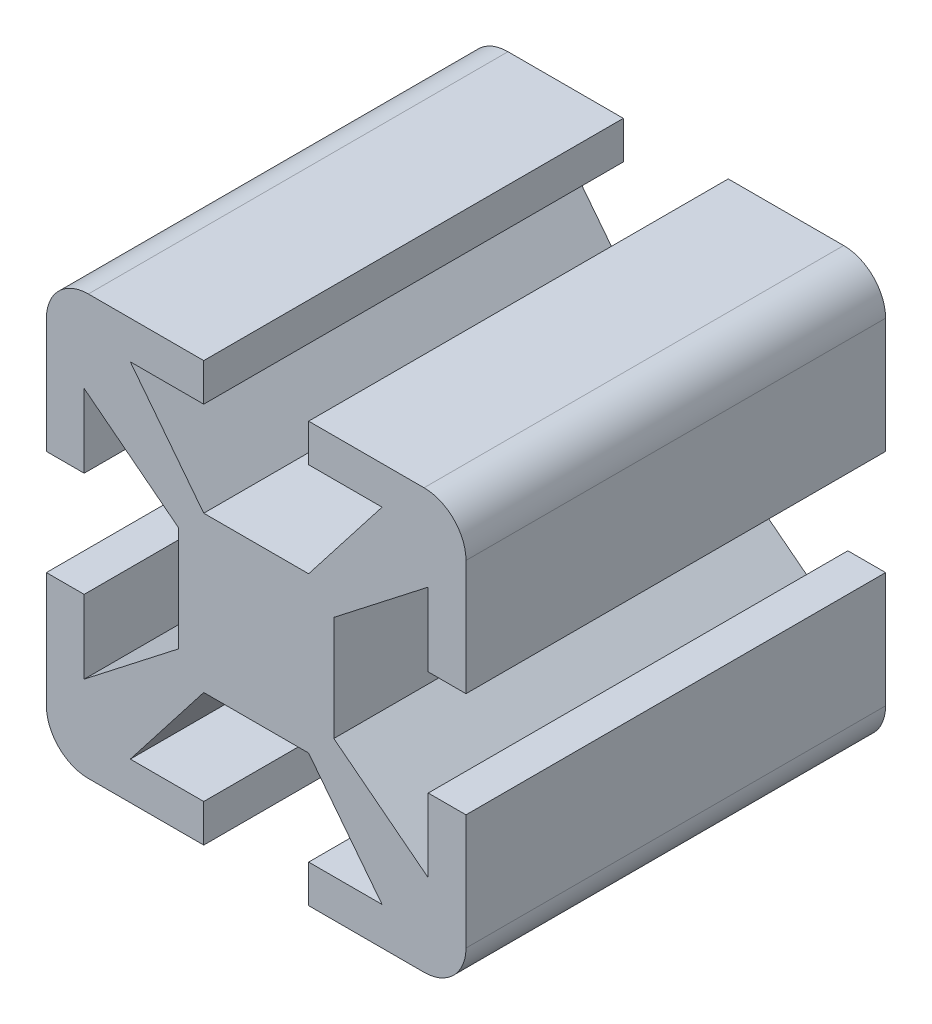
SolidWorks part; units mm, degrees
ref_plane "Plan de face" through (0, 0, 0) normal (0, 0, 1) x (1, 0, 0)
ref_plane "Plan de dessus" through (0, 0, 0) normal (0, 1, 0) x (1, 0, 0)
ref_plane "Plan de droite" through (0, 0, 0) normal (1, 0, 0) x (0, 0, -1)
sketch "Esquisse1" plane through (0, 0, 0) normal (0, 0, 1) x (1, 0, 0)
  line L0 (-10, 8) -> (-10, -8)
  line L1 (-8, 10) -> (8, 10)
  line L2 (-8, -10) -> (8, -10)
  line L3 (10, 8) -> (10, -8)
  line L4 (-8, 8) -> (8, -8) construction
  line L5 (8, 8) -> (-8, -8) construction
  arc A0 (-8, 10) -> (-10, 8) centre (-8, 8) ccw
  arc A1 (8, 10) -> (10, 8) centre (8, 8) cw
  arc A2 (10, -8) -> (8, -10) centre (8, -8) cw
  arc A3 (-8, -10) -> (-10, -8) centre (-8, -8) cw
  point P12 (0, 0)
  dimension "D1" = 2
  dimension "D2" = 2
  dimension "D4" = 2
  dimension "D3" = 20
extrude "Extrusion1" add sketch "Esquisse1" along normal blind 20
sketch "Esquisse3" plane through (0, 0, 20) normal (0, 0, 1) x (1, 0, 0)
  line L0 (10, 2.5) -> (8.2, 2.5)
  line L2 (8.2, 2.5) -> (8.2, 6)
  line L3 (3.7, 2.5) -> (3.7, -2.5)
  line L4 (8.2, -6) -> (8.2, -2.5)
  line L5 (8.2, -2.5) -> (10, -2.5)
  line L6 (10, -8) -> (10, 8) construction
  line L7 (8.2, 6) -> (3.7, 2.5)
  line L8 (10, 2.5) -> (10, -2.5)
  line L9 (8.2, -6) -> (3.7, -2.5)
  point P4 (10, 0)
  point P10 (10, 0)
  dimension "D1" = 5
  dimension "D2" = 1.8
  dimension "D3" = 6.3
  dimension "D4" = 12
  dimension "D5" = 5
extrude "Enlèv. mat.-Extru.1" cut sketch "Esquisse3" against normal blind 300
sketch "Esquisse4" plane through (0, 0, 20) normal (0, 0, 1) x (1, 0, 0)
  line L0 (-10, 2.5) -> (-8.2, 2.5)
  line L1 (-10, 8) -> (-10, -8) construction
  line L2 (-8.2, 2.5) -> (-8.2, 6)
  line L3 (-8.2, 6) -> (-3.7, 2.5)
  line L4 (-3.7, 2.5) -> (-3.7, -2.5)
  line L5 (-8.2, -2.5) -> (-8.2, -6)
  line L6 (-8.2, -2.5) -> (-10, -2.5)
  line L7 (-10, -2.5) -> (-10, 2.5)
  line L8 (-8.2, -6) -> (-3.7, -2.5)
  dimension "D1" = 5
  dimension "D2" = 5
  dimension "D3" = 1.8
  dimension "D4" = 6.3
sketch "Esquisse5" plane through (0, 0, 20) normal (0, 0, 1) x (1, 0, 0)
  line L0 (-2.5, 10) -> (-2.5, 8.2)
  line L1 (8, 10) -> (-8, 10) construction
  line L2 (-2.5, 8.2) -> (-6, 8.2)
  line L3 (-6, 8.2) -> (-2.5, 3.7)
  line L4 (-2.5, 3.7) -> (2.5, 3.7)
  line L5 (2.5, 3.7) -> (6, 8.2)
  line L6 (6, 8.2) -> (2.5, 8.2)
  line L7 (2.5, 8.2) -> (2.5, 10)
  line L8 (2.5, 10) -> (-2.5, 10)
  point P4 (0, 10)
  dimension "D1" = 5
  dimension "D2" = 6.3
  dimension "D3" = 1.8
  dimension "D4" = 12
extrude "Enlèv. mat.-Extru.3" cut sketch "Esquisse5" against normal blind 300
sketch "Esquisse6" plane through (0, 0, 20) normal (0, 0, 1) x (1, 0, 0)
  line L0 (-2.5, -10) -> (-2.5, -8.2)
  line L1 (-8, -10) -> (8, -10) construction
  line L2 (-2.5, -8.2) -> (-6, -8.2)
  line L3 (-6, -8.2) -> (-2.5, -3.7)
  line L4 (-2.5, -3.7) -> (2.5, -3.7)
  line L5 (6, -8.2) -> (2.5, -8.2)
  line L6 (2.5, -8.2) -> (2.5, -10)
  line L7 (2.5, -10) -> (-2.5, -10)
  line L8 (2.5, 8.2) -> (2.5, 10) construction
  line L9 (-2.5, 10) -> (-2.5, 8.2) construction
  line L10 (2.5, -3.7) -> (6, -8.2)
  dimension "D1" = 6.3
  dimension "D2" = 12
  dimension "D3" = 1.8
extrude "Enlèv. mat.-Extru.4" cut sketch "Esquisse6" against normal through all
extrude "Enlèv. mat.-Extru.7" cut sketch "Esquisse4" against normal through all
